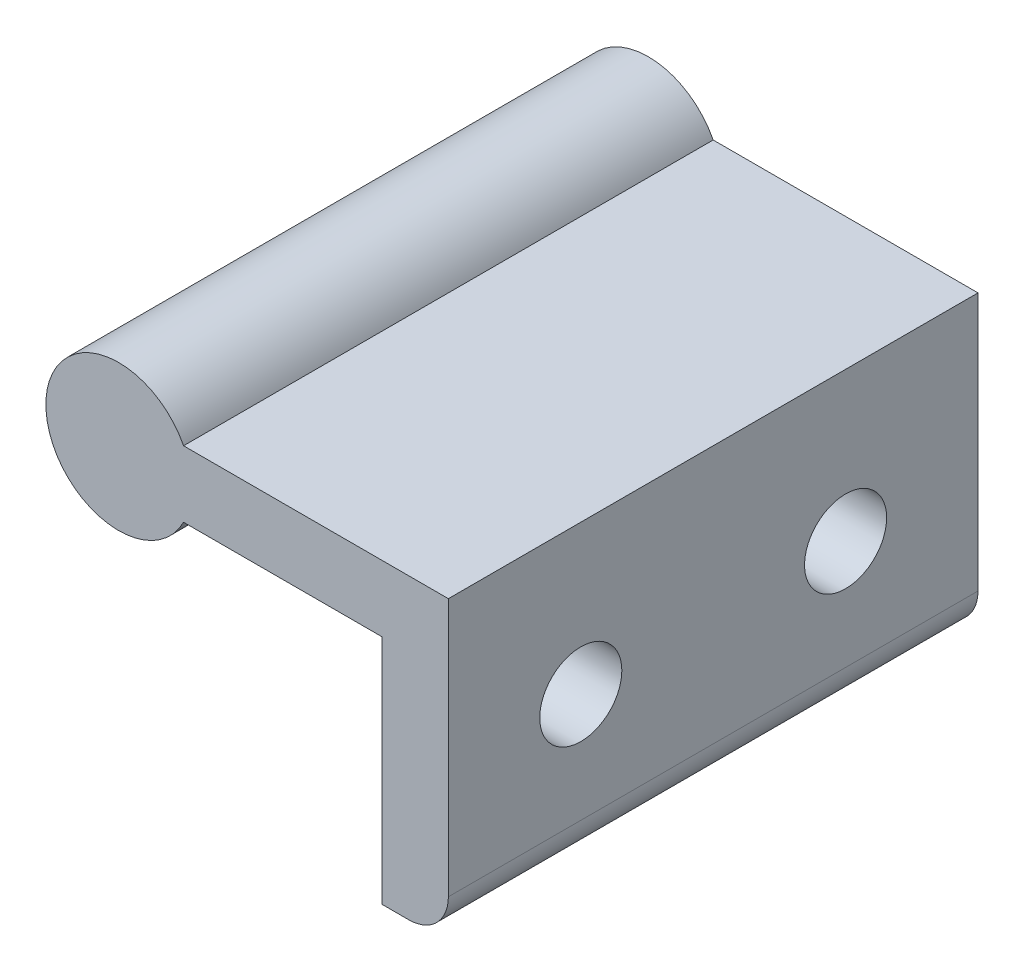
SolidWorks part; units mm, degrees
ref_plane "Front Plane" through (0, 0, 0) normal (0, 0, 1) x (1, 0, 0)
ref_plane "Top Plane" through (0, 0, 0) normal (0, 1, 0) x (1, 0, 0)
ref_plane "Right Plane" through (0, 0, 0) normal (1, 0, 0) x (0, 0, -1)
sketch "Sketch1" plane through (0, 0, 0) normal (0, 0, 1) x (1, 0, 0)
  line L0 (0.6248, 0) -> (79.6749, 0) construction
  line L2 (4.899, 2.5) -> (24.899, 2.5)
  line L3 (4.899, 2.5) -> (4.899, -2.5)
  line L4 (4.899, -2.5) -> (24.899, -2.5)
  line L5 (24.899, 2.5) -> (24.899, -2.5)
  line L6 (24.899, -2.5) -> (19.899, -2.5)
  line L7 (24.899, -2.5) -> (24.899, -20)
  line L8 (24.899, -20) -> (19.899, -20)
  line L9 (19.899, -2.5) -> (19.899, -20)
  circle A0 centre (0, 0) radius 5.5
  point P9 (24.899, 0)
  dimension "D1" = 11
  dimension "D2" = 5
  dimension "D3" = 20
  dimension "D4" = 17.5
  dimension "D5" = 5
extrude "Boss-Extrude1" add sketch "Sketch1" along normal blind 40
sketch "Sketch2" plane through (24.899, 0, 0) normal (1, 0, 0) x (0, 0, -1)
  line L0 (-40, -8.75) -> (0, -8.75) construction
  line L1 (-40, 2.5) -> (-40, -20) construction
  line L2 (0, 2.5) -> (0, -20) construction
  circle A0 centre (-30, -8.75) radius 3.1
  circle A1 centre (-10, -8.75) radius 3.1
  dimension "D1" = 6.2
  dimension "D2" = 6.2
  dimension "D3" = 10
  dimension "D4" = 10
extrude "Cut-Extrude1" cut sketch "Sketch2" against normal blind 10
fillet "Fillet1" radius 3 1 edges at (24.899, -20, 20)
